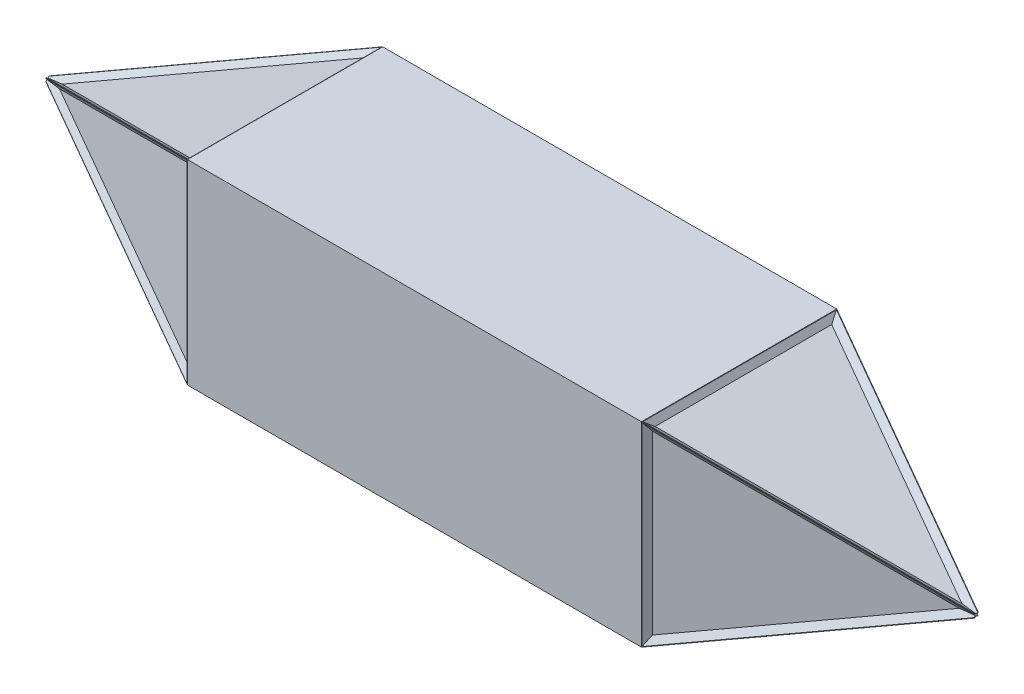
SolidWorks part; units mm, degrees
ref_plane "Plan de face" through (0, 0, 0) normal (0, 0, 1) x (1, 0, 0)
ref_plane "Plan de dessus" through (0, 0, 0) normal (0, 1, 0) x (1, 0, 0)
ref_plane "Plan de droite" through (0, 0, 0) normal (1, 0, 0) x (0, 0, -1)
sketch "Esquisse3" plane through (0, 0, 0) normal (0, 0, 1) x (1, 0, 0)
  line L1 (0, 0) -> (1000, 0)
  line L2 (0, 0) -> (0, 430)
  line L3 (0, 430) -> (1000, 430)
  line L4 (1000, 0) -> (1000, 430)
  dimension "D1" = 1000
  dimension "D2" = 430
extrude "Boss.-Extru.2" add sketch "Esquisse3" along normal blind 430
sketch "Esquisse4" plane through (0, 0, 0) normal (-1, 0, 0) x (0, 0, 1)
  line L1 (0, 0) -> (430, 0)
  line L2 (0, 0) -> (0, 430)
  line L3 (0, 430) -> (430, 430)
  line L4 (430, 0) -> (430, 430)
extrude "Boss.-Extru.3" add sketch "Esquisse4" along normal blind 522.4 draft 22
sketch "Esquisse5" plane through (1000, 0, 0) normal (1, 0, 0) x (0, 0, -1)
  line L1 (-430, 430) -> (0, 430)
  line L2 (-430, 430) -> (-430, 0)
  line L3 (-430, 0) -> (0, 0)
  line L4 (0, 430) -> (0, 0)
extrude "Boss.-Extru.4" add sketch "Esquisse5" along normal blind 522 draft 22
sketch "Esquisse6" plane through (-149.3515, 0, 369.6581) normal (-0.3746, 0, 0.9272) x (0.9272, 0, 0.3746)
  line L0 (160.0808, 428.5575) -> (160.0808, 1.4425)
  line L1 (160.0808, 1.4425) -> (-410.004, 215)
  line L2 (-410.004, 215) -> (160.0808, 428.5575)
  line L3 (161.0808, 430) -> (161.0808, 0) construction
  line L4 (-402.3457, 211.0633) -> (161.0808, 0) construction
  line L5 (-402.3457, 218.9367) -> (161.0808, 430) construction
  dimension "D1" = 1
  dimension "D2" = 1
  dimension "D3" = 1
extrude "Enlèv. mat.-Extru.1" cut sketch "Esquisse6" against normal blind 10 draft 53
sketch "Esquisse7" plane through (-149.3515, 369.6581, 0) normal (-0.3746, 0.9272, 0) x (0.9272, 0.3746, 0)
  line L0 (160.0808, -428.5575) -> (160.0808, -1.4425)
  line L1 (160.0808, -1.4425) -> (-410.004, -215)
  line L2 (-410.004, -215) -> (160.0808, -428.5575)
  line L3 (-402.3457, -218.9367) -> (161.0808, -430) construction
  line L4 (-402.3457, -211.0633) -> (161.0808, 0) construction
  line L5 (161.0808, -430) -> (161.0808, 0) construction
  dimension "D1" = 1
  dimension "D2" = 1
  dimension "D3" = 1
extrude "Enlèv. mat.-Extru.2" cut sketch "Esquisse7" against normal blind 10 draft 53
sketch "Esquisse8" plane through (0, 0, 0) normal (-0.3746, 0, -0.9272) x (-0.9272, 0, 0.3746)
  line L0 (1, 428.5575) -> (1, 1.4425)
  line L1 (1, 1.4425) -> (571.0848, 215)
  line L2 (571.0848, 215) -> (1, 428.5575)
  line L3 (0, 430) -> (0, 0) construction
  line L4 (563.4265, 218.9367) -> (0, 430) construction
  line L6 (563.4265, 211.0633) -> (0, 0) construction
  dimension "D1" = 1
  dimension "D2" = 1
  dimension "D3" = 1
extrude "Enlèv. mat.-Extru.3" cut sketch "Esquisse8" against normal blind 10 draft 53
sketch "Esquisse9" plane through (0, 0, 0) normal (-0.3746, -0.9272, 0) x (0.9272, -0.3746, 0)
  line L0 (-571.0848, 215) -> (-1, 1.4425)
  line L1 (-571.0848, 215) -> (-1, 428.5575)
  line L2 (-1, 428.5575) -> (-1, 1.4425)
  line L3 (-563.4265, 211.0633) -> (0, 0) construction
  line L4 (0, 430) -> (0, 0) construction
  line L5 (-563.4265, 218.9367) -> (0, 430) construction
  dimension "D1" = 1
  dimension "D2" = 1
  dimension "D3" = 1
extrude "Enlèv. mat.-Extru.4" cut sketch "Esquisse9" against normal blind 10 draft 53
sketch "Esquisse12" plane through (140.3301, -347.3292, 0) normal (0.3746, -0.9272, 0) x (-0.9272, -0.3746, 0)
  line L0 (-928.1839, -428.5575) -> (-928.1839, -1.4425)
  line L2 (-1498.2687, -215) -> (-928.1839, -428.5575)
  line L3 (-1498.2687, -215) -> (-928.1839, -1.4425)
  line L4 (-1490.179, -210.9017) -> (-927.1839, 0) construction
  line L5 (-1490.179, -219.0983) -> (-927.1839, -430) construction
  line L6 (-927.1839, -430) -> (-927.1839, 0) construction
  dimension "D1" = 1
  dimension "D2" = 1
  dimension "D3" = 1
extrude "Enlèv. mat.-Extru.7" cut sketch "Esquisse12" against normal blind 10 draft 53
sketch "Esquisse13" plane through (289.6816, 0, 716.9872) normal (0.3746, 0, 0.9272) x (0.9272, 0, -0.3746)
  line L0 (767.103, 428.5575) -> (767.103, 1.4425)
  line L1 (767.103, 1.4425) -> (1337.1878, 215)
  line L2 (1337.1878, 215) -> (767.103, 428.5575)
  line L5 (1329.0982, 219.0983) -> (766.103, 430) construction
  line L6 (1329.0982, 210.9017) -> (766.103, 0) construction
  line L7 (766.103, 0) -> (766.103, 430) construction
  dimension "D1" = 1
  dimension "D2" = 1
  dimension "D3" = 1
extrude "Enlèv. mat.-Extru.8" cut sketch "Esquisse13" against normal blind 10 draft 53
sketch "Esquisse14" plane through (289.6816, 716.9872, 0) normal (0.3746, 0.9272, 0) x (0.9272, -0.3746, 0)
  line L0 (767.103, -1.4425) -> (767.103, -428.5575)
  line L1 (767.103, -428.5575) -> (1337.1878, -215)
  line L2 (1337.1878, -215) -> (767.103, -1.4425)
  line L3 (1329.0982, -219.0983) -> (766.103, -430) construction
  line L4 (1329.0982, -210.9017) -> (766.103, 0) construction
  line L5 (766.103, -430) -> (766.103, 0) construction
  dimension "D1" = 1
  dimension "D2" = 1
  dimension "D3" = 1
extrude "Enlèv. mat.-Extru.9" cut sketch "Esquisse14" against normal blind 10 draft 53
sketch "Esquisse15" plane through (140.3301, 0, -347.3292) normal (0.3746, 0, -0.9272) x (-0.9272, 0, -0.3746)
  line L0 (-928.1839, 428.5575) -> (-928.1839, 1.4425)
  line L1 (-928.1839, 1.4425) -> (-1498.2687, 215)
  line L2 (-1498.2687, 215) -> (-928.1839, 428.5575)
  line L3 (-927.1839, 0) -> (-927.1839, 430) construction
  line L4 (-1490.179, 219.0983) -> (-927.1839, 430) construction
  line L5 (-1490.179, 210.9017) -> (-927.1839, 0) construction
  dimension "D1" = 1
  dimension "D2" = 1
  dimension "D3" = 1
extrude "Enlèv. mat.-Extru.10" cut sketch "Esquisse15" against normal blind 10 draft 53
ref_plane "Plan1" through (499.8, 0, 0) normal (1, 0, 0) x (0, 0, -1)
ref_plane "Plan2" through (0, 215, 215) normal (0, 0.7071, 0.7071) x (1, 0, 0)
